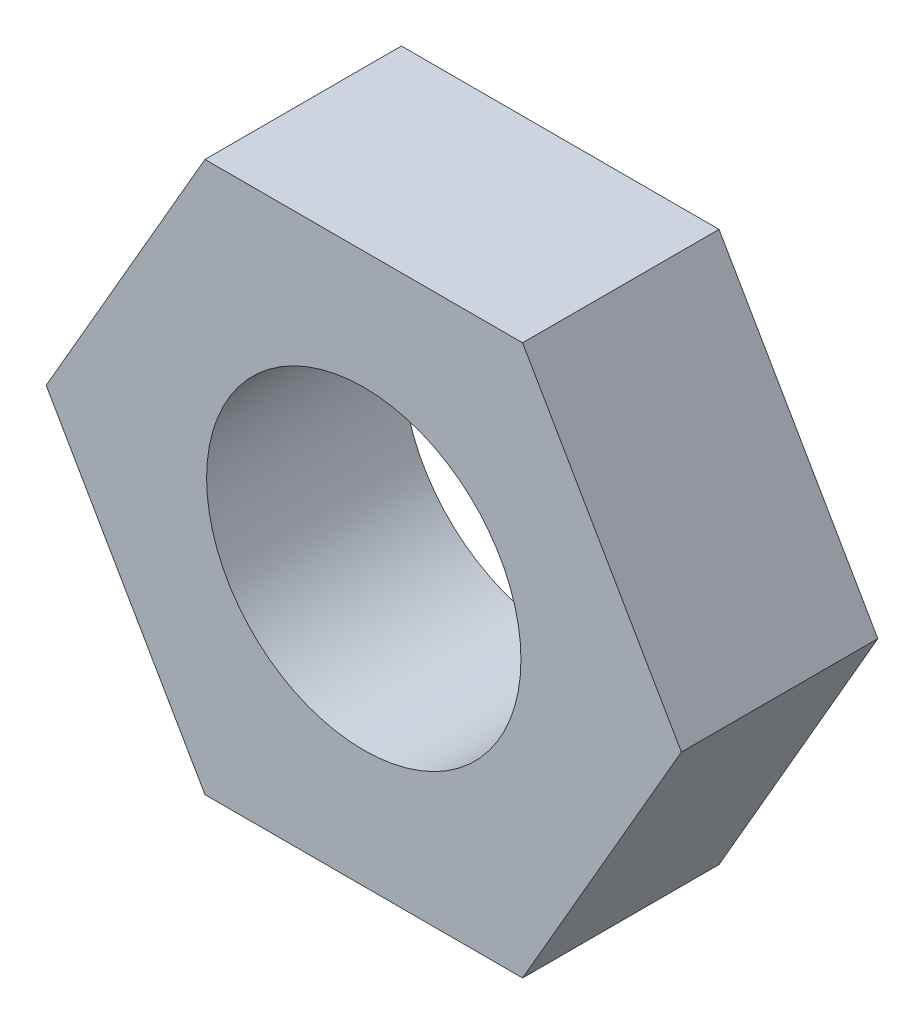
SolidWorks part; units mm, degrees
ref_plane "Alzado" through (0, 0, 0) normal (0, 0, 1) x (1, 0, 0)
ref_plane "Planta" through (0, 0, 0) normal (0, 1, 0) x (1, 0, 0)
ref_plane "Vista lateral" through (0, 0, 0) normal (1, 0, 0) x (0, 0, -1)
sketch "Croquis1" plane through (0, 0, 0) normal (0, 0, 1) x (1, 0, 0)
  line L1 (4.0415, 0) -> (2.0207, 3.5)
  line L2 (2.0207, 3.5) -> (-2.0207, 3.5)
  line L3 (-2.0207, 3.5) -> (-4.0415, 0)
  line L4 (-4.0415, 0) -> (-2.0207, -3.5)
  line L5 (-2.0207, -3.5) -> (2.0207, -3.5)
  line L6 (2.0207, -3.5) -> (4.0415, 0)
  circle A0 centre (0, 0) radius 3.5 construction
  circle A1 centre (0, 0) radius 2
  dimension "D1" = 7
  dimension "D2" = 4
extrude "Saliente-Extruir1" add sketch "Croquis1" along normal blind 2.5
